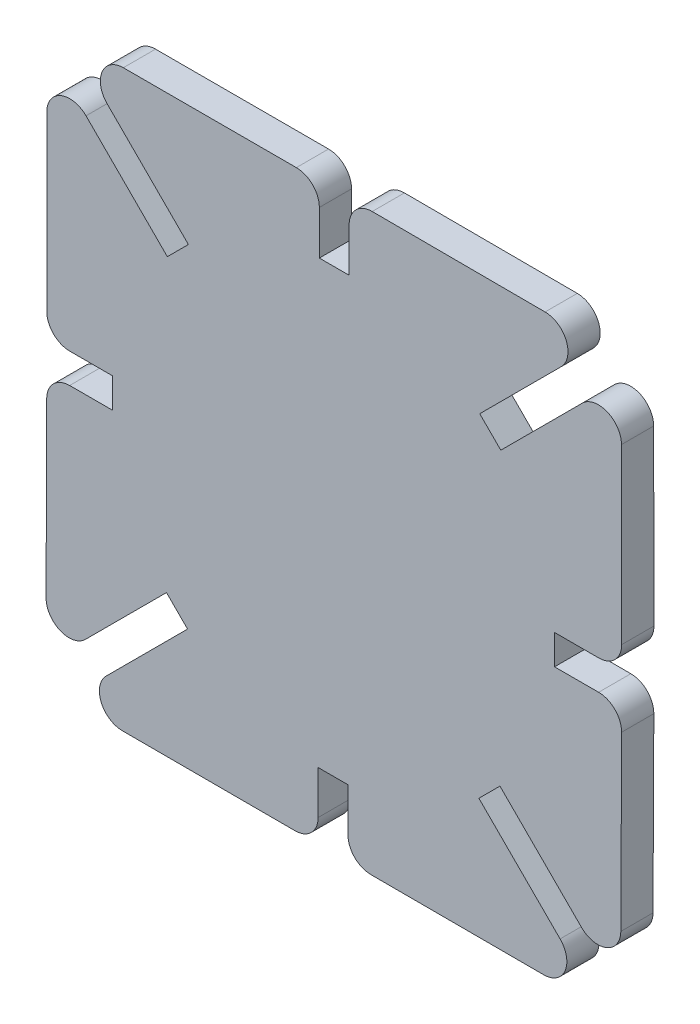
SolidWorks part; units mm, degrees
ref_plane "Front Plane" through (0, 0, 0) normal (0, 0, 1) x (1, 0, 0)
ref_plane "Top Plane" through (0, 0, 0) normal (0, 1, 0) x (1, 0, 0)
ref_plane "Right Plane" through (0, 0, 0) normal (1, 0, 0) x (0, 0, -1)
sketch "Sketch2" plane through (0, 0, 0) normal (0, 0, 1) x (1, 0, 0)
  line L7 (25, 25) -> (-25, 25) construction
  line L11 (25, -25) -> (25, 25) construction
  line L12 (0, 0) -> (-25, 25) construction
  line L16 (0, 0) -> (-25, 0) construction
  line L17 (-25, 25) -> (-25, -25) construction
  line L21 (-25, -25) -> (25, -25) construction
  line L22 (-23.1686, 25) -> (-12.6825, 14.5139)
  line L23 (-12.6825, 14.5139) -> (-14.5139, 12.6825)
  line L24 (-14.5139, 12.6825) -> (-25, 23.1686)
  line L25 (-1.295, 19.1871) -> (-1.295, 25)
  line L26 (1.295, 25) -> (1.295, 19.1871)
  line L27 (1.295, 19.1871) -> (-1.295, 19.1871)
  line L28 (12.6516, 14.4394) -> (23.1377, 24.9255)
  line L29 (24.9691, 23.0941) -> (14.483, 12.608)
  line L30 (14.483, 12.608) -> (12.6516, 14.4394)
  line L31 (19.1563, 1.2205) -> (25, 1.2205)
  line L32 (25, -1.3695) -> (19.1563, -1.3695)
  line L33 (19.1563, -1.3695) -> (19.1563, 1.2205)
  line L34 (14.4085, -12.7262) -> (24.8946, -23.2122)
  line L35 (23.0632, -25.0437) -> (12.5771, -14.5576)
  line L36 (12.5771, -14.5576) -> (14.4085, -12.7262)
  line L37 (1.1896, -19.2308) -> (1.1896, -25)
  line L38 (-1.4004, -25) -> (-1.4004, -19.2308)
  line L39 (-1.4004, -19.2308) -> (1.1896, -19.2308)
  line L40 (-12.757, -14.483) -> (-23.2431, -24.9691)
  line L41 (-25.0745, -23.1377) -> (-14.5884, -12.6516)
  line L42 (-14.5884, -12.6516) -> (-12.757, -14.483)
  line L43 (-19.2616, -1.2641) -> (-25, -1.2641)
  line L44 (-25, 1.3259) -> (-19.2616, 1.3259)
  line L45 (-19.2616, 1.3259) -> (-19.2616, -1.2641)
  line L46 (-23.1686, 25) -> (-1.295, 25)
  line L47 (1.295, 25) -> (23.1377, 24.9255)
  line L48 (24.9691, 23.0941) -> (25, 1.2205)
  line L49 (24.8946, -23.2122) -> (25, -1.3695)
  line L50 (23.0632, -25.0437) -> (1.1896, -25)
  line L51 (-23.2431, -24.9691) -> (-1.4004, -25)
  line L52 (-25.0745, -23.1377) -> (-25, -1.2641)
  line L53 (-25, 23.1686) -> (-25, 1.3259)
  circle A0 centre (0, 0) radius 19.2308 construction
  point P5 (0, 25)
extrude "Boss-Extrude1" add sketch "Sketch2" along normal mid plane 2.8
fillet "Fillet1" radius 2 16 edges at (-25, 1.3259, 0) (-25, -1.2641, 0) (-25.0745, -23.1377, 0) (-23.2431, -24.9691, 0) (1.1896, -25, 0) (-1.4004, -25, 0) (23.0632, -25.0437, 0) (24.8946, -23.2122, 0) (25, -1.3695, 0) (25, 1.2205, 0) (24.9691, 23.0941, 0) (23.1377, 24.9255, 0) (1.295, 25, 0) (-1.295, 25, 0) (-23.1686, 25, 0) (-25, 23.1686, 0)
equation "\"Length\"= 50mm"
equation "\"Width\"= 50mm"
equation "\"Mat_Thickness\"= 2.8mm"
equation "\"Kerf\"= 0.21mm"
equation "\"D1@Boss-Extrude1\"=\"Mat_Thickness\""
equation "\"D1@Sketch2\"=\"Mat_Thickness\"-\"Kerf\""
equation "\"D3@Sketch2\"=\"Width\"/1.3"
equation "\"D1@Fillet1\"=\"Width\"/25"
equation "\"D2@Sketch2\"=\"Width\""
